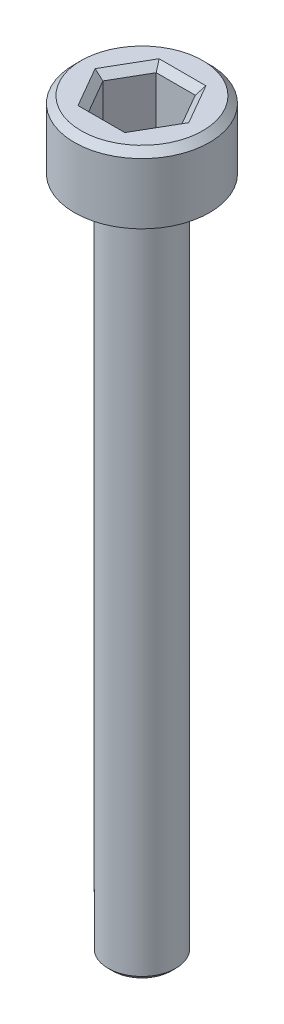
SolidWorks part; units mm, degrees
ref_plane "Front Plane" through (0, 0, 0) normal (0, 0, 1) x (1, 0, 0)
ref_plane "Top Plane" through (0, 0, 0) normal (0, 1, 0) x (1, 0, 0)
ref_plane "Right Plane" through (0, 0, 0) normal (1, 0, 0) x (0, 0, -1)
sketch "Sketch1" plane through (0, 0, 0) normal (0, 1, 0) x (1, 0, 0)
  circle A0 centre (0, 0) radius 3
  dimension "D1" = 6
extrude "Boss-Extrude1" add sketch "Sketch1" along normal blind 3
chamfer "Chamfer1" distance 0.3 angle 45 1 edges at (0, 3, 3)
sketch "Sketch2" plane through (0, 3, 0) normal (0, 1, 0) x (1, 0, 0)
  line L1 (1.7321, 0) -> (0.866, 1.5)
  line L2 (0.866, 1.5) -> (-0.866, 1.5)
  line L3 (-0.866, 1.5) -> (-1.7321, 0)
  line L4 (-1.7321, 0) -> (-0.866, -1.5)
  line L5 (-0.866, -1.5) -> (0.866, -1.5)
  line L6 (0.866, -1.5) -> (1.7321, 0)
  circle A0 centre (0, 0) radius 1.5 construction
  dimension "D1" = 3
extrude "Cut-Extrude1" cut sketch "Sketch2" against normal blind 2.5
chamfer "Chamfer2" distance 0.3 angle 45 6 edges at (1.299, 3, -0.75) (1.299, 3, 0.75) (0, 3, 1.5) (-1.299, 3, 0.75) (-1.299, 3, -0.75) (0, 3, -1.5)
sketch "Sketch3" plane through (0, 0, 0) normal (0, -1, 0) x (1, 0, 0)
  circle A0 centre (0, 0) radius 1.5
  dimension "D1" = 3
extrude "Boss-Extrude2" add sketch "Sketch3" along normal blind 30
chamfer "Chamfer3" distance 0.2 angle 45 1 edges at (0, -30, -1.5)
